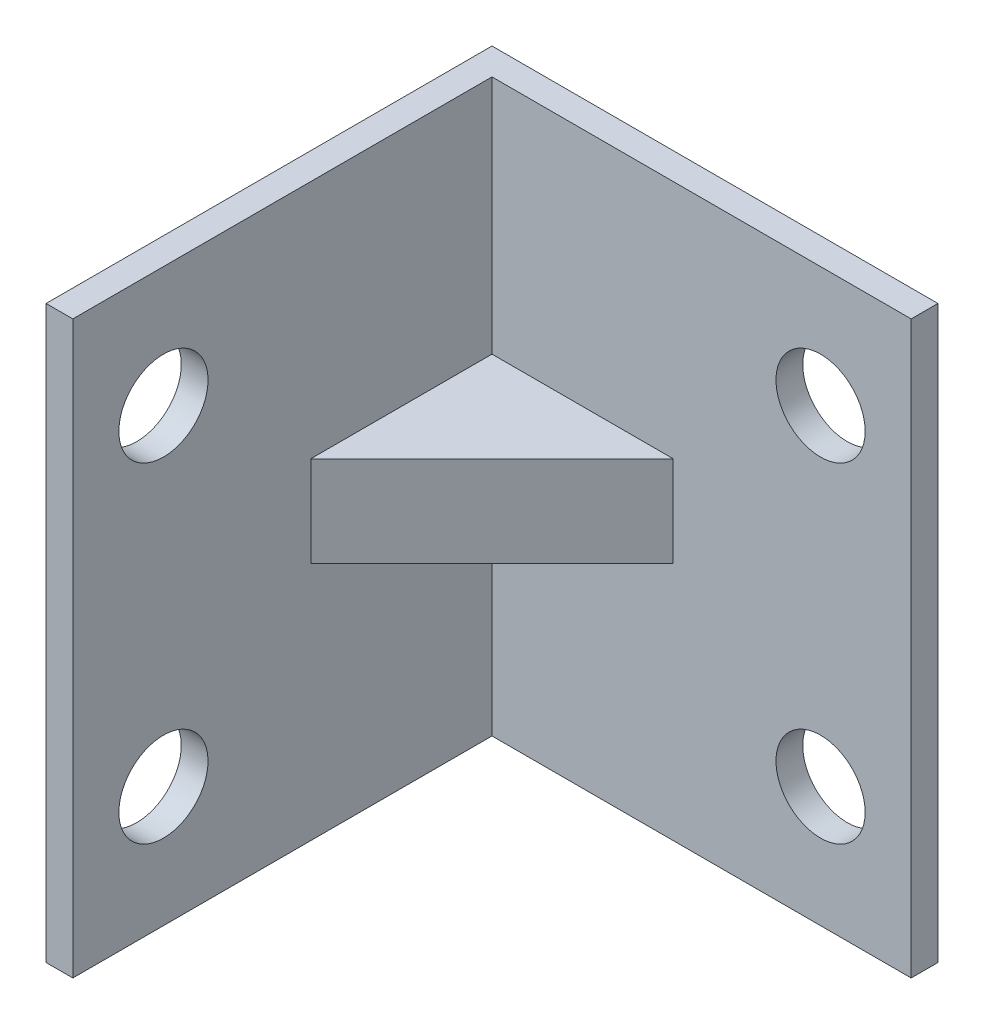
SolidWorks part; units mm, degrees
ref_plane "Front Plane" through (0, 0, 0) normal (0, 0, 1) x (1, 0, 0)
ref_plane "Top Plane" through (0, 0, 0) normal (0, 1, 0) x (1, 0, 0)
ref_plane "Right Plane" through (0, 0, 0) normal (1, 0, 0) x (0, 0, -1)
sketch "Sketch1" plane through (0, 0, 0) normal (0, 0, 1) x (1, 0, 0)
  line L0 (12.5, 0) -> (-12.5, 0) construction
  line L1 (-12.5, 16) -> (12.5, 16) construction
  line L2 (-12.5, 16) -> (-12.5, -16) construction
  line L3 (-12.5, -16) -> (12.5, -16) construction
  line L4 (12.5, 16) -> (12.5, -16) construction
  line L5 (-12.5, 16) -> (12.5, -16) construction
  line L6 (-12.5, -16) -> (12.5, 16) construction
  line L8 (-12.5, 16) -> (-12.5, -16)
  line L9 (-12.5, -16) -> (12.5, -16)
  line L10 (-12.5, 16) -> (12.5, 16)
  line L11 (12.5, 16) -> (12.5, -16)
  line L12 (7.42, 9.25) -> (7.42, -9.25) construction
  circle A3 centre (7.42, -9.25) radius 2.5
  circle A4 centre (7.42, 9.25) radius 2.5
  point P7 (0, 0)
  point P10 (7.42, 0)
  dimension "D1" = 18.5
  dimension "D4" = 5
  dimension "D5" = 5
  dimension "D2" = 25
  dimension "D3" = 32
  dimension "D6" = 5.08
extrude "Boss-Extrude1" add sketch "Sketch1" along normal blind 1.5
sketch "Sketch2" plane through (-12.5, 0, 0) normal (-1, 0, 0) x (0, 0, 1)
  line L0 (1.5, 16) -> (0, 16) construction
  line L1 (0, -16) -> (25, -16)
  line L2 (0, -16) -> (0, 16)
  line L3 (0, 16) -> (25, 16)
  line L4 (25, -16) -> (25, 16)
  line L5 (0, -16) -> (25, 16) construction
  line L6 (0, 16) -> (25, -16) construction
  line L7 (25, 0) -> (0, 0) construction
  line L8 (19.92, -9.25) -> (19.92, 9.25) construction
  circle A0 centre (19.92, -9.25) radius 2.5
  circle A1 centre (19.92, 9.25) radius 2.5
  point P4 (12.5, 0)
  point P12 (19.92, 0)
  dimension "D4" = 5
  dimension "D5" = 5
  dimension "D1" = 25
  dimension "D2" = 18.5
  dimension "D3" = 5.08
extrude "Boss-Extrude2" add sketch "Sketch2" against normal blind 1.5
sketch "Sketch3" plane through (0, 0, 0) normal (0, 1, 0) x (1, 0, 0)
  line L0 (-11, -25) -> (-11, -1.5) construction
  line L1 (-11, -25) -> (-11, -1.5) construction
  line L2 (12.5, -1.5) -> (-11, -1.5) construction
  line L3 (12.5, -1.5) -> (-11, -1.5) construction
  line L4 (-11, -1.5) -> (-11, -11.66)
  line L5 (-11, -11.66) -> (-0.84, -1.5)
  line L6 (-0.84, -1.5) -> (-11, -1.5)
  dimension "D1" = 45
  dimension "D2" = 10.16
extrude "Boss-Extrude3" add sketch "Sketch3" along normal blind 2.54 and the other way blind 2.54
